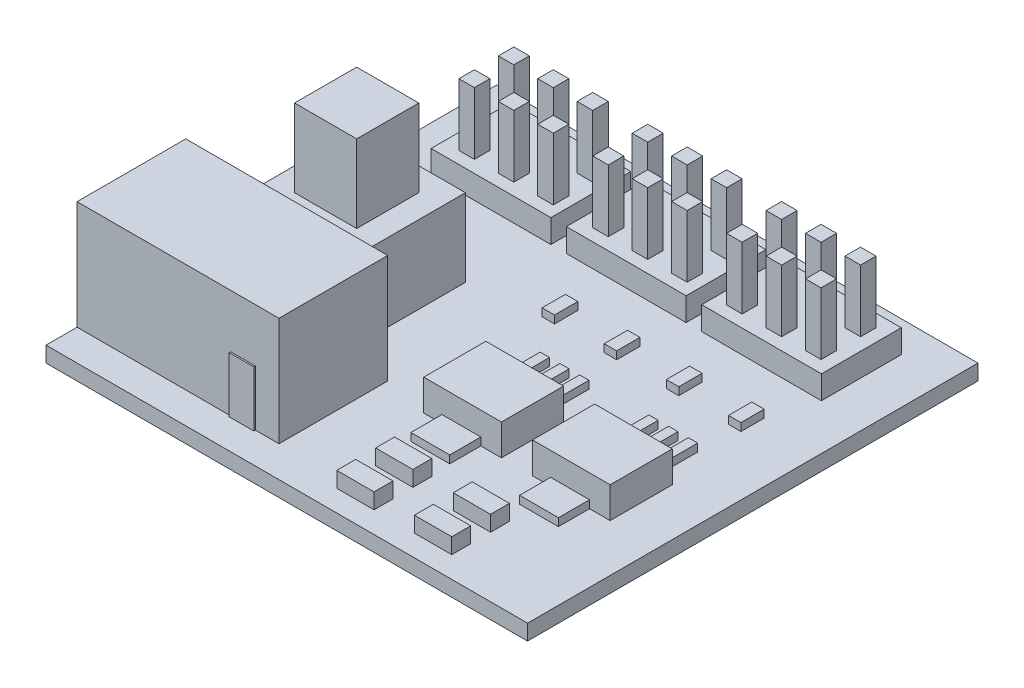
SolidWorks part; units mm, degrees
ref_plane "Front Plane" through (0, 0, 0) normal (0, 0, 1) x (1, 0, 0)
ref_plane "Top Plane" through (0, 0, 0) normal (0, 1, 0) x (1, 0, 0)
ref_plane "Right Plane" through (0, 0, 0) normal (1, 0, 0) x (0, 0, -1)
sketch "Sketch1" plane through (0, 0, 0) normal (0, 1, 0) x (1, 0, 0)
  line L1 (0, 0) -> (31, 0)
  line L2 (0, 0) -> (0, 29)
  line L3 (0, 29) -> (31, 29)
  line L4 (31, 0) -> (31, 29)
  dimension "D1" = 31
  dimension "D2" = 29
extrude "Boss-Extrude1" add sketch "Sketch1" along normal blind 1
sketch "Sketch2" plane through (0, 0, 0) normal (-1, 0, 0) x (0, 0, 1)
  line L0 (-29, 0) -> (0, 0) construction
  line L1 (-9, 0) -> (-2, 0)
  line L2 (-9, 0) -> (-9, 8)
  line L3 (-9, 8) -> (-2, 8)
  line L4 (-2, 0) -> (-2, 8)
  line L5 (0, 1) -> (0, 0) construction
  dimension "D1" = 7
  dimension "D2" = 8
  dimension "D3" = 2
extrude "Boss-Extrude2" add sketch "Sketch2" against normal blind 13
sketch "Sketch3" plane through (0, 1, 0) normal (0, 1, 0) x (1, 0, 0)
  line L0 (0, 9) -> (13, 9) construction
  line L1 (10, 17) -> (3, 17)
  line L2 (10, 17) -> (10, 10)
  line L3 (10, 10) -> (3, 10)
  line L4 (3, 17) -> (3, 10)
  line L5 (0, 29) -> (0, 9) construction
  dimension "D1" = 7
  dimension "D2" = 7
  dimension "D3" = 1
  dimension "D4" = 3
extrude "Boss-Extrude3" add sketch "Sketch3" along normal blind 5
sketch "Sketch4" plane through (0, 6, 0) normal (0, 1, 0) x (1, 0, 0)
  line L0 (3, 17) -> (3, 10) construction
  line L1 (8.5, 15.5) -> (4.5, 15.5)
  line L2 (8.5, 15.5) -> (8.5, 11.5)
  line L3 (8.5, 11.5) -> (4.5, 11.5)
  line L4 (4.5, 15.5) -> (4.5, 11.5)
  line L5 (3, 10) -> (10, 10) construction
  dimension "D1" = 4
  dimension "D2" = 4
  dimension "D3" = 1.5
  dimension "D4" = 1.5
extrude "Boss-Extrude4" add sketch "Sketch4" along normal blind 5
sketch "Sketch5" plane through (0, 0, 0) normal (-1, 0, 0) x (0, 0, 1)
  line L0 (-2, 4.5) -> (-9, 4.5) construction
  line L1 (-2, 1) -> (-2, 8) construction
  line L2 (-9, 8) -> (-9, 1) construction
  line L3 (-5.5, 8) -> (-5.5, 0) construction
  line L4 (-2, 8) -> (-9, 8) construction
  line L5 (-29, 0) -> (0, 0) construction
  circle A0 centre (-5.5, 4.5) radius 2.75
  point P8 (0, 0)
  point P9 (-5.5, 4.1852)
  point P16 (-5.5, 8)
  point P17 (-5.5, 4.5)
  dimension "D1" = 5.5
extrude "Cut-Extrude1" cut sketch "Sketch5" against normal blind 8
sketch "Sketch6" plane through (0, 0, -2) normal (0, 0, 1) x (1, 0, 0)
  line L0 (13, 1) -> (0, 1) construction
  line L1 (9.8886, 1) -> (11.4798, 1)
  line L2 (9.8886, 1) -> (9.8886, 4.5744)
  line L3 (9.8886, 4.5744) -> (11.4798, 4.5744)
  line L4 (11.4798, 1) -> (11.4798, 4.5744)
extrude "Boss-Extrude5" add sketch "Sketch6" along normal blind 0.1
sketch "Sketch7" plane through (8, 0, 0) normal (-1, 0, 0) x (0, 0, 1)
  circle A0 centre (-5.5, 4.5) radius 0.8796
  circle A1 centre (-5.5, 4.5) radius 2.75 construction
extrude "Boss-Extrude6" add sketch "Sketch7" along normal blind 8
fillet "Fillet2" radius 0.5 1 edges at (0, 4.5, -4.6204)
sketch "Sketch8" plane through (0, 1, 0) normal (0, 1, 0) x (1, 0, 0)
  line L0 (11.64, 27) -> (19.35, 27)
  line L1 (2.93, 27) -> (10.64, 27)
  line L2 (2.93, 27) -> (2.93, 21.86)
  line L3 (2.93, 21.86) -> (10.64, 21.86)
  line L4 (10.64, 27) -> (10.64, 21.86)
  line L5 (19.35, 27) -> (19.35, 21.86)
  line L6 (11.64, 21.86) -> (19.35, 21.86)
  line L7 (11.64, 27) -> (11.64, 21.86)
  line L8 (20.35, 27) -> (28.06, 27)
  line L9 (28.06, 27) -> (28.06, 21.86)
  line L10 (20.35, 21.86) -> (28.06, 21.86)
  line L11 (20.35, 27) -> (20.35, 21.86)
  line L12 (0, 29) -> (0, 9) construction
  line L14 (31, 29) -> (0, 29) construction
  dimension "D1" = 5.14
  dimension "D2" = 7.71
  dimension "D4" = 2.93
  dimension "D5" = 2
  dimension "D3" = 3
extrude "Boss-Extrude7" add sketch "Sketch8" along normal blind 1.5
sketch "Sketch9" plane through (0, 2.5, 0) normal (0, 1, 0) x (1, 0, 0)
  line L0 (7.4715, 26.185) -> (6.4715, 26.185)
  line L1 (4.9315, 26.185) -> (3.9315, 26.185)
  line L2 (4.9315, 26.185) -> (4.9315, 25.185)
  line L3 (4.9315, 25.185) -> (3.9315, 25.185)
  line L4 (3.9315, 26.185) -> (3.9315, 25.185)
  line L5 (7.4715, 26.185) -> (7.4715, 25.185)
  line L6 (7.4715, 25.185) -> (6.4715, 25.185)
  line L7 (6.4715, 26.185) -> (6.4715, 25.185)
  line L8 (10.0115, 26.185) -> (9.0115, 26.185)
  line L9 (10.0115, 26.185) -> (10.0115, 25.185)
  line L10 (10.0115, 25.185) -> (9.0115, 25.185)
  line L11 (9.0115, 26.185) -> (9.0115, 25.185)
  line L12 (2.93, 21.86) -> (10.64, 21.86) construction
  line L13 (3.9315, 23.645) -> (4.9315, 23.645)
  line L14 (3.9315, 23.645) -> (3.9315, 22.645)
  line L15 (3.9315, 22.645) -> (4.9315, 22.645)
  line L16 (4.9315, 23.645) -> (4.9315, 22.645)
  line L17 (13.5515, 23.645) -> (13.5515, 22.645)
  line L18 (6.4715, 23.645) -> (7.4715, 23.645)
  line L19 (7.4715, 23.645) -> (7.4715, 22.645)
  line L20 (6.4715, 22.645) -> (7.4715, 22.645)
  line L21 (6.4715, 23.645) -> (6.4715, 22.645)
  line L22 (9.0115, 23.645) -> (10.0115, 23.645)
  line L23 (10.0115, 23.645) -> (10.0115, 22.645)
  line L24 (9.0115, 22.645) -> (10.0115, 22.645)
  line L25 (9.0115, 23.645) -> (9.0115, 22.645)
  line L26 (12.5515, 22.645) -> (13.5515, 22.645)
  line L27 (12.5515, 23.645) -> (12.5515, 22.645)
  line L28 (18.6315, 26.185) -> (18.6315, 25.185)
  line L29 (18.6315, 26.185) -> (17.6315, 26.185)
  line L30 (17.6315, 26.185) -> (17.6315, 25.185)
  line L31 (18.6315, 25.185) -> (17.6315, 25.185)
  line L32 (17.6315, 23.645) -> (18.6315, 23.645)
  line L33 (18.6315, 23.645) -> (18.6315, 22.645)
  line L34 (17.6315, 22.645) -> (18.6315, 22.645)
  line L35 (17.6315, 23.645) -> (17.6315, 22.645)
  line L36 (16.0915, 23.645) -> (16.0915, 22.645)
  line L37 (15.0915, 22.645) -> (16.0915, 22.645)
  line L38 (15.0915, 23.645) -> (15.0915, 22.645)
  line L39 (15.0915, 23.645) -> (16.0915, 23.645)
  line L40 (16.0915, 25.185) -> (15.0915, 25.185)
  line L41 (16.0915, 26.185) -> (16.0915, 25.185)
  line L42 (16.0915, 26.185) -> (15.0915, 26.185)
  line L43 (15.0915, 26.185) -> (15.0915, 25.185)
  line L44 (13.5515, 26.185) -> (13.5515, 25.185)
  line L45 (13.5515, 25.185) -> (12.5515, 25.185)
  line L46 (12.5515, 26.185) -> (12.5515, 25.185)
  line L47 (13.5515, 26.185) -> (12.5515, 26.185)
  line L48 (12.5515, 23.645) -> (13.5515, 23.645)
  line L49 (22.1715, 23.645) -> (22.1715, 22.645)
  line L50 (21.1715, 22.645) -> (22.1715, 22.645)
  line L51 (21.1715, 23.645) -> (21.1715, 22.645)
  line L52 (27.2515, 26.185) -> (27.2515, 25.185)
  line L53 (27.2515, 26.185) -> (26.2515, 26.185)
  line L54 (26.2515, 26.185) -> (26.2515, 25.185)
  line L55 (27.2515, 25.185) -> (26.2515, 25.185)
  line L56 (26.2515, 23.645) -> (27.2515, 23.645)
  line L57 (27.2515, 23.645) -> (27.2515, 22.645)
  line L58 (26.2515, 22.645) -> (27.2515, 22.645)
  line L59 (26.2515, 23.645) -> (26.2515, 22.645)
  line L60 (24.7115, 23.645) -> (24.7115, 22.645)
  line L61 (23.7115, 22.645) -> (24.7115, 22.645)
  line L62 (23.7115, 23.645) -> (23.7115, 22.645)
  line L63 (23.7115, 23.645) -> (24.7115, 23.645)
  line L64 (24.7115, 25.185) -> (23.7115, 25.185)
  line L65 (24.7115, 26.185) -> (24.7115, 25.185)
  line L66 (24.7115, 26.185) -> (23.7115, 26.185)
  line L67 (23.7115, 26.185) -> (23.7115, 25.185)
  line L68 (22.1715, 26.185) -> (22.1715, 25.185)
  line L69 (22.1715, 25.185) -> (21.1715, 25.185)
  line L70 (21.1715, 26.185) -> (21.1715, 25.185)
  line L71 (22.1715, 26.185) -> (21.1715, 26.185)
  line L72 (21.1715, 23.645) -> (22.1715, 23.645)
  dimension "D1" = 1
  dimension "D2" = 1
  dimension "D4" = 2.54
  dimension "D5" = 1
  dimension "D6" = 1
  dimension "D7" = 0.785
  dimension "D8" = 3
  dimension "D3" = 3
  dimension "D9" = 3
extrude "Boss-Extrude8" add sketch "Sketch9" along normal blind 4
sketch "Sketch10" plane through (0, 1, 0) normal (0, 1, 0) x (1, 0, 0)
  line L0 (18.3861, 19.0508) -> (18.3861, 17.5508)
  line L1 (14.3861, 19.0508) -> (15.1861, 19.0508)
  line L2 (14.3861, 19.0508) -> (14.3861, 17.5508)
  line L3 (14.3861, 17.5508) -> (15.1861, 17.5508)
  line L4 (15.1861, 19.0508) -> (15.1861, 17.5508)
  line L5 (18.3861, 19.0508) -> (19.1861, 19.0508)
  line L6 (19.1861, 19.0508) -> (19.1861, 17.5508)
  line L7 (18.3861, 17.5508) -> (19.1861, 17.5508)
  line L8 (22.3861, 19.0508) -> (22.3861, 17.5508)
  line L9 (22.3861, 19.0508) -> (23.1861, 19.0508)
  line L10 (23.1861, 19.0508) -> (23.1861, 17.5508)
  line L11 (22.3861, 17.5508) -> (23.1861, 17.5508)
  line L12 (26.3861, 19.0508) -> (26.3861, 17.5508)
  line L13 (26.3861, 19.0508) -> (27.1861, 19.0508)
  line L14 (27.1861, 19.0508) -> (27.1861, 17.5508)
  line L15 (26.3861, 17.5508) -> (27.1861, 17.5508)
  dimension "D1" = 1.5
  dimension "D2" = 0.8
  dimension "D3" = 4
extrude "Boss-Extrude9" add sketch "Sketch10" along normal blind 0.5
sketch "Sketch11" plane through (0, 1, 0) normal (0, 1, 0) x (1, 0, 0)
  line L0 (27.9438, 12.3748) -> (22.9438, 12.3748)
  line L1 (20.9438, 12.3748) -> (15.9438, 12.3748)
  line L2 (20.9438, 12.3748) -> (20.9438, 8.3748)
  line L3 (20.9438, 8.3748) -> (15.9438, 8.3748)
  line L4 (15.9438, 12.3748) -> (15.9438, 8.3748)
  line L5 (27.9438, 12.3748) -> (27.9438, 8.3748)
  line L6 (27.9438, 8.3748) -> (22.9438, 8.3748)
  line L7 (22.9438, 12.3748) -> (22.9438, 8.3748)
  dimension "D1" = 5
  dimension "D2" = 4
  dimension "D3" = 2
extrude "Boss-Extrude10" add sketch "Sketch11" along normal blind 2
sketch "Sketch12" plane through (0, 1, 0) normal (0, 1, 0) x (1, 0, 0)
  line L0 (20.9438, 12.3748) -> (15.9438, 12.3748) construction
  line L1 (16.7953, 12.3748) -> (17.3953, 12.3748)
  line L2 (16.7953, 12.3748) -> (16.7953, 15.0175)
  line L3 (16.7953, 15.0175) -> (17.3953, 15.0175)
  line L4 (17.3953, 12.3748) -> (17.3953, 15.0175)
  line L5 (23.7953, 12.3748) -> (24.3953, 12.3748)
  line L6 (18.0653, 12.3748) -> (18.6653, 12.3748)
  line L7 (18.0653, 12.3748) -> (18.0653, 15.0175)
  line L8 (18.0653, 15.0175) -> (18.6653, 15.0175)
  line L9 (18.6653, 12.3748) -> (18.6653, 15.0175)
  line L10 (19.3353, 12.3748) -> (19.9353, 12.3748)
  line L11 (19.3353, 12.3748) -> (19.3353, 15.0175)
  line L12 (19.3353, 15.0175) -> (19.9353, 15.0175)
  line L13 (19.9353, 12.3748) -> (19.9353, 15.0175)
  line L14 (23.7953, 12.3748) -> (23.7953, 15.0175)
  line L15 (23.7953, 15.0175) -> (24.3953, 15.0175)
  line L16 (24.3953, 12.3748) -> (24.3953, 15.0175)
  line L17 (25.0653, 12.3748) -> (25.6653, 12.3748)
  line L18 (25.0653, 12.3748) -> (25.0653, 15.0175)
  line L19 (25.0653, 15.0175) -> (25.6653, 15.0175)
  line L20 (25.6653, 12.3748) -> (25.6653, 15.0175)
  line L21 (26.3353, 12.3748) -> (26.9353, 12.3748)
  line L22 (26.3353, 12.3748) -> (26.3353, 15.0175)
  line L23 (26.3353, 15.0175) -> (26.9353, 15.0175)
  line L24 (26.9353, 12.3748) -> (26.9353, 15.0175)
  dimension "D1" = 0.6
  dimension "D2" = 0.6
  dimension "D3" = 0.6
  dimension "D4" = 1.27
  dimension "D5" = 1.27
  dimension "D6" = 2
extrude "Boss-Extrude11" add sketch "Sketch12" along normal blind 0.5
sketch "Sketch13" plane through (0, 1, 0) normal (0, 1, 0) x (1, 0, 0)
  line L0 (15.9438, 8.3748) -> (20.9438, 8.3748) construction
  line L1 (17.1153, 8.3748) -> (19.6153, 8.3748)
  line L2 (17.1153, 8.3748) -> (17.1153, 6.3748)
  line L3 (17.1153, 6.3748) -> (19.6153, 6.3748)
  line L4 (19.6153, 8.3748) -> (19.6153, 6.3748)
  line L5 (24.1153, 8.3748) -> (26.6153, 8.3748)
  line L6 (24.1153, 8.3748) -> (24.1153, 6.3748)
  line L7 (24.1153, 6.3748) -> (26.6153, 6.3748)
  line L8 (26.6153, 8.3748) -> (26.6153, 6.3748)
  line L9 (18.3653, 6.3748) -> (18.3653, 8.3748) construction
  line L10 (18.3653, 15.0175) -> (18.3653, 12.3559) construction
  line L11 (18.6653, 15.0175) -> (18.0653, 15.0175) construction
  dimension "D1" = 2.5
  dimension "D2" = 2
  dimension "D3" = 2
extrude "Boss-Extrude12" add sketch "Sketch13" along normal blind 0.5
sketch "Sketch14" plane through (0, 1, 0) normal (0, 1, 0) x (1, 0, 0)
  line L0 (24.7411, 5.0978) -> (22.34, 5.0978)
  line L1 (19.7411, 5.0978) -> (17.34, 5.0978)
  line L2 (19.7411, 5.0978) -> (19.7411, 3.8785)
  line L3 (19.7411, 3.8785) -> (17.34, 3.8785)
  line L4 (17.34, 5.0978) -> (17.34, 3.8785)
  line L5 (24.7411, 5.0978) -> (24.7411, 3.8785)
  line L6 (24.7411, 3.8785) -> (22.34, 3.8785)
  line L7 (22.34, 5.0978) -> (22.34, 3.8785)
  line L8 (24.7411, 2.5978) -> (22.34, 2.5978)
  line L9 (24.7411, 2.5978) -> (24.7411, 1.3785)
  line L10 (24.7411, 1.3785) -> (22.34, 1.3785)
  line L11 (22.34, 2.5978) -> (22.34, 1.3785)
  line L12 (19.7411, 2.5978) -> (17.34, 2.5978)
  line L13 (19.7411, 2.5978) -> (19.7411, 1.3785)
  line L14 (19.7411, 1.3785) -> (17.34, 1.3785)
  line L15 (17.34, 2.5978) -> (17.34, 1.3785)
  dimension "D1" = 2
  dimension "D2" = 2
extrude "Boss-Extrude13" add sketch "Sketch14" along normal blind 1
